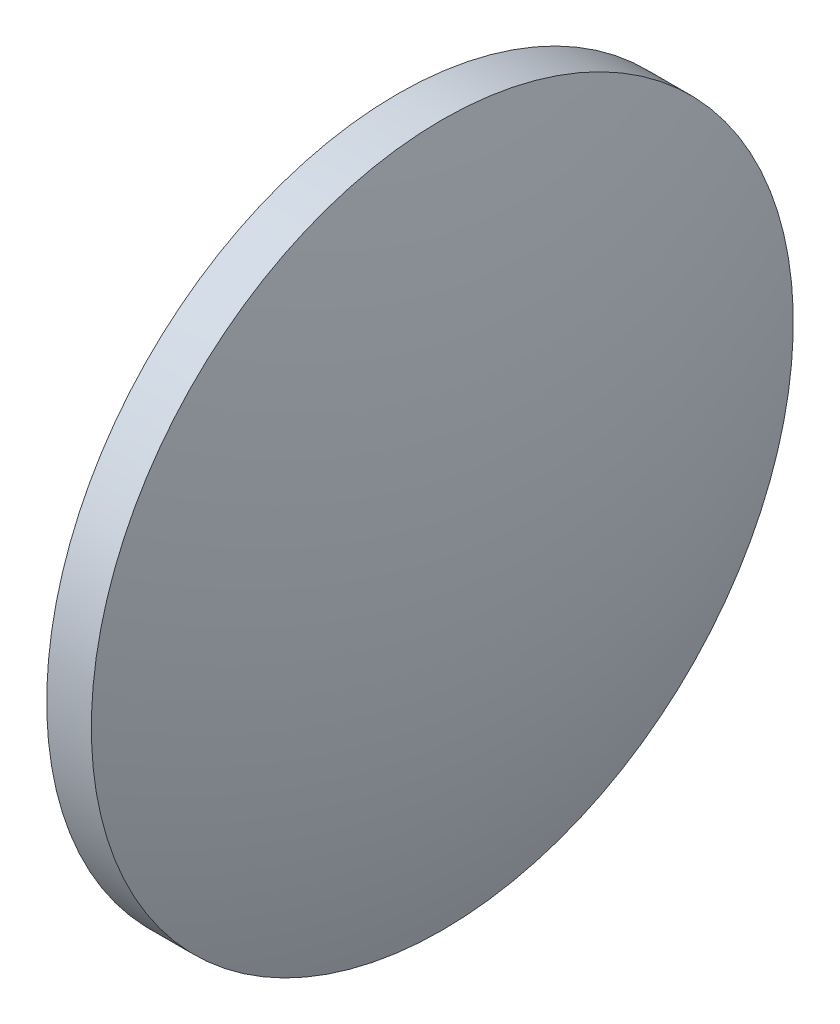
SolidWorks part; units mm, degrees
ref_plane "前视基准面" through (0, 0, 0) normal (0, 0, 1) x (1, 0, 0)
ref_plane "上视基准面" through (0, 0, 0) normal (0, 1, 0) x (1, 0, 0)
ref_plane "右视基准面" through (0, 0, 0) normal (1, 0, 0) x (0, 0, -1)
sketch "草图1" plane through (0, 0, 0) normal (0, 0, 1) x (1, 0, 0)
  line L0 (84.3016, 60.3505) -> (85.8916, 60.3505)
  line L1 (85.8916, 60.3505) -> (85.8916, 35.3505)
  line L2 (85.8916, 35.3505) -> (84.3016, 35.3505)
  line L3 (84.3016, 35.3505) -> (84.3016, 60.3505)
  line L4 (81.213, 47.8505) -> (89.3486, 47.8505) construction
  arc A0 (84.3016, 60.3505) -> (84.3016, 35.3505) centre (123.2858, 47.8505) ccw
  arc A1 (85.8916, 35.3505) -> (85.8916, 60.3505) centre (46.9075, 47.8505) ccw
  dimension "D1" = 1.59
  dimension "D2" = 25
revolve "旋转1" add sketch "草图1" angle 360 about L4
